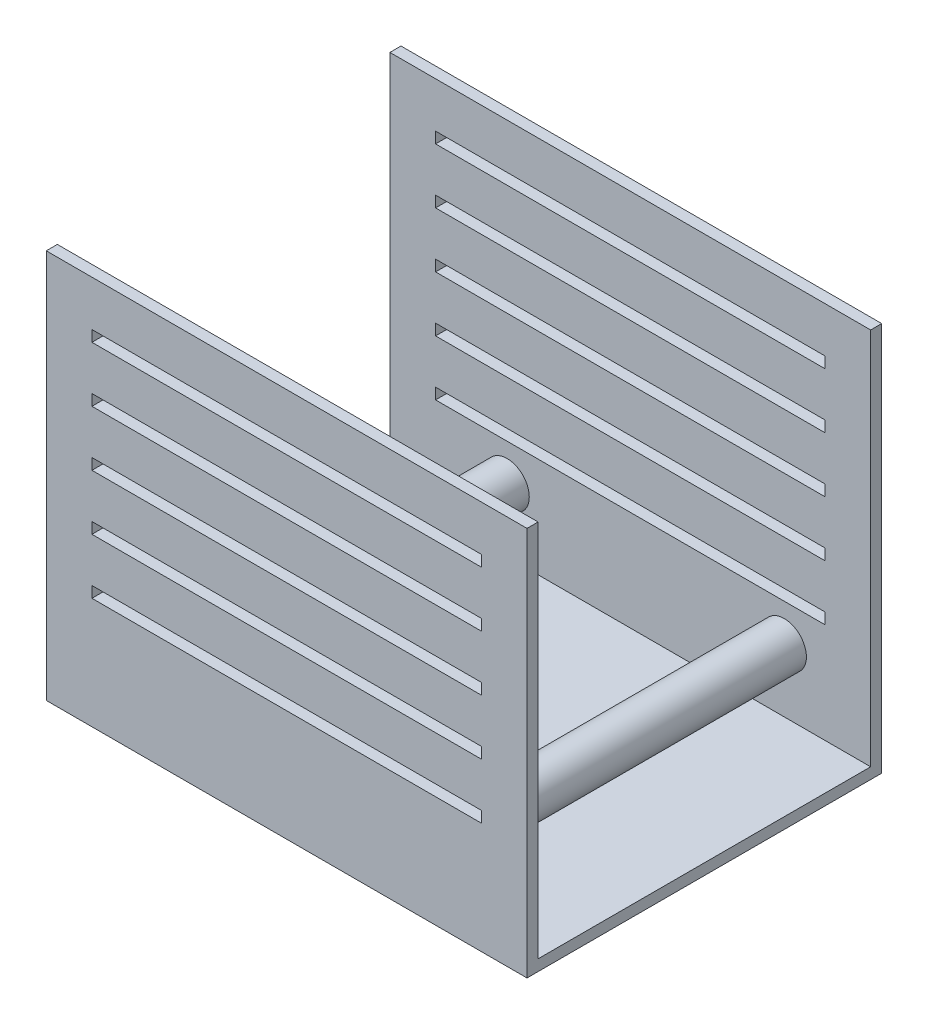
SolidWorks part; units mm, degrees
ref_plane "Front Plane" through (0, 0, 0) normal (0, 0, 1) x (1, 0, 0)
ref_plane "Top Plane" through (0, 0, 0) normal (0, 1, 0) x (1, 0, 0)
ref_plane "Right Plane" through (0, 0, 0) normal (1, 0, 0) x (0, 0, -1)
sketch "Sketch1" plane through (0, 0, 0) normal (0, 0, 1) x (1, 0, 0)
  circle A0 centre (-25, -30.44) radius 4 construction
  circle A1 centre (-25, -30.44) radius 4
  circle A2 centre (25, -30.44) radius 4 construction
  circle A3 centre (25, -30.44) radius 4
extrude "Boss-Extrude1" add sketch "Sketch1" against normal mid plane 60
sketch "Sketch2" plane through (0, 0, 30) normal (0, 0, 1) x (1, 0, 0)
  line L1 (40.5924, -41.8091) -> (-46.1461, -41.8091)
  line L2 (40.5924, -41.8091) -> (40.5924, 26.4451)
  line L3 (40.5924, 26.4451) -> (-46.1461, 26.4451)
  line L4 (-46.1461, -41.8091) -> (-46.1461, 26.4451)
extrude "Boss-Extrude2" add sketch "Sketch2" along normal blind 2
sketch "Sketch4" plane through (0, 0, 32) normal (0, 0, 1) x (1, 0, 0)
  line L0 (-37.9045, 17.2675) -> (32.3509, 17.2675)
  line L1 (-37.9045, 7.2675) -> (32.3509, 7.2675)
  line L2 (-37.9045, -2.7325) -> (32.3509, -2.7325)
  line L3 (-37.9045, -12.7325) -> (32.3509, -12.7325)
  line L4 (-37.9045, -22.7325) -> (32.3509, -22.7325)
  line L6 (-37.9045, 17.2675) -> (-46.1461, 17.2675) construction
  line L7 (-46.1461, 26.4451) -> (-46.1461, -41.8091) construction
  line L8 (32.3509, 17.2675) -> (40.5924, 17.2675) construction
  line L9 (40.5924, -41.8091) -> (40.5924, 26.4451) construction
  line L10 (-37.9045, -32.7325) -> (32.3509, -32.7325) [skipped]
  dimension "D1" = 6
extrude "Cut-Extrude-Thin1" cut sketch "Sketch4" against normal up to next (2 mm away) thin thin type mid plane wall 2
mirror "Mirror1" about plane through (0, 0, 0) normal (0, 0, 1) of "Cut-Extrude-Thin1", "Boss-Extrude2"
sketch "Sketch3" plane through (0, -41.8091, 0) normal (0, -1, 0) x (1, 0, 0)
  line L1 (-46.1461, 32) -> (40.5924, 32)
  line L2 (-46.1461, 32) -> (-46.1461, -32)
  line L3 (-46.1461, -32) -> (40.5924, -32)
  line L4 (40.5924, 32) -> (40.5924, -32)
extrude "Boss-Extrude3" add sketch "Sketch3" along normal blind 2
